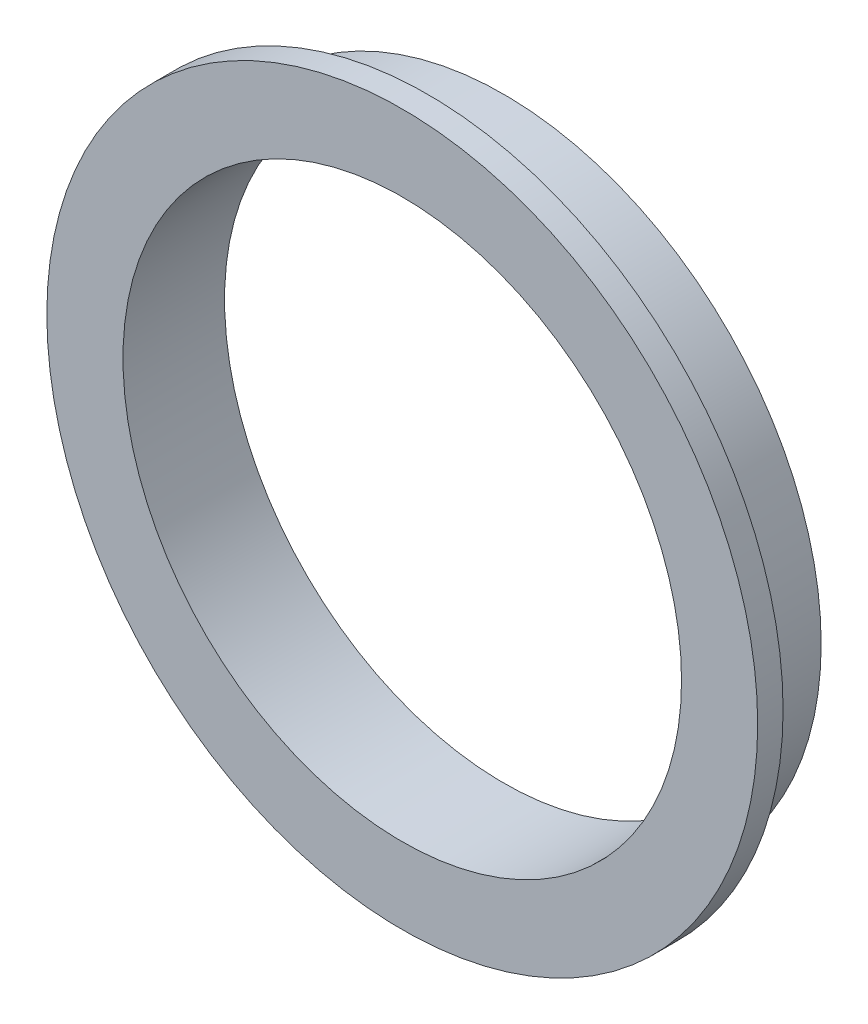
SolidWorks part; units mm, degrees
material "6061-T6 (SS)"
ref_plane "Front Plane" through (0, 0, 0) normal (0, 0, 1) x (1, 0, 0)
ref_plane "Top Plane" through (0, 0, 0) normal (0, 1, 0) x (1, 0, 0)
ref_plane "Right Plane" through (0, 0, 0) normal (1, 0, 0) x (0, 0, -1)
sketch "Sketch2" plane through (0, 0, 0) normal (1, 0, 0) x (0, 0, -1)
  line L0 (0, 0) -> (44.2866, 0) construction
  line L1 (0, 69.85) -> (25.4, 69.85)
  line L2 (0, 69.85) -> (0, 88.9)
  line L3 (0, 88.9) -> (6.35, 88.9)
  line L4 (6.35, 88.9) -> (6.35, 79.375)
  line L5 (6.35, 79.375) -> (25.4, 79.375)
  line L6 (25.4, 79.375) -> (25.4, 76.2)
  line L7 (25.4, 76.2) -> (3.175, 76.2)
  line L8 (3.175, 76.2) -> (3.175, 73.025)
  line L9 (3.175, 73.025) -> (25.4, 73.025)
  line L10 (25.4, 73.025) -> (25.4, 69.85)
  dimension "D1" = 146.05
  dimension "D2" = 3.175
  dimension "D3" = 152.4
  dimension "D4" = 177.8
  dimension "D5" = 3.175
  dimension "D6" = 6.35
  dimension "D7" = 25.4
revolve "Revolve1" add sketch "Sketch2" angle 360 about L0
